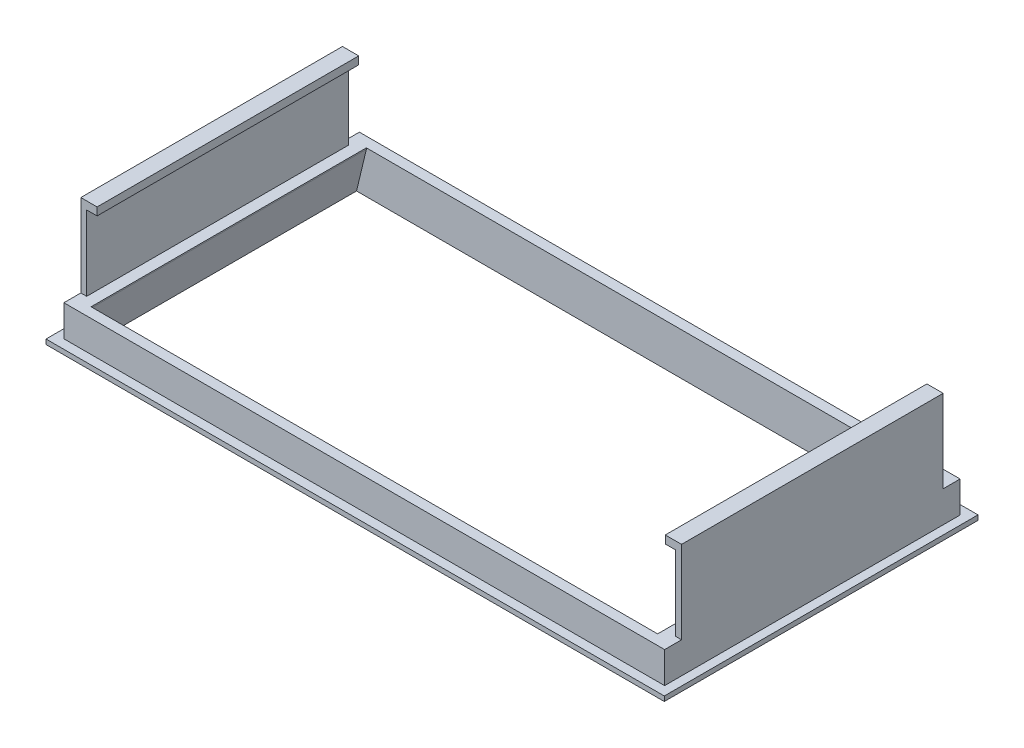
SolidWorks part; units mm, degrees
ref_plane "Front" through (0, 0, 0) normal (0, 0, 1) x (1, 0, 0)
ref_plane "Top" through (0, 0, 0) normal (0, 1, 0) x (1, 0, 0)
ref_plane "Right" through (0, 0, 0) normal (1, 0, 0) x (0, 0, -1)
sketch "Sketch1" plane through (0, 0, 0) normal (0, 1, 0) x (1, 0, 0)
  line L1 (-47.5, 24.1) -> (47.5, 24.1)
  line L2 (-47.5, 24.1) -> (-47.5, -24.1)
  line L3 (-47.5, -24.1) -> (47.5, -24.1)
  line L4 (47.5, 24.1) -> (47.5, -24.1)
  dimension "D1" = 95
  dimension "D2" = 48.2
  dimension "D3" = 24.1
  dimension "D4" = 47.5
extrude "Boss-Extrude2" add sketch "Sketch1" along normal blind 1.7
sketch "Sketch3" plane through (0, 1.7, 0) normal (0, 1, 0) x (1, 0, 0)
  line L1 (-46.15, 22.7) -> (46.15, 22.7)
  line L2 (-46.15, 22.7) -> (-46.15, -22.7)
  line L3 (-46.15, -22.7) -> (46.15, -22.7)
  line L4 (46.15, 22.7) -> (46.15, -22.7)
  dimension "D1" = 45.4
  dimension "D2" = 92.3
  dimension "D3" = 46.15
  dimension "D4" = 22.7
extrude "Boss-Extrude3" add sketch "Sketch3" along normal blind 4.8
sketch "Sketch4" plane through (0, 6.5, 0) normal (0, 1, 0) x (-1, 0, 0)
  line L1 (43.525, -21.15) -> (-43.525, -21.15)
  line L2 (43.525, -21.15) -> (43.525, 21.15)
  line L3 (43.525, 21.15) -> (-43.525, 21.15)
  line L4 (-43.525, -21.15) -> (-43.525, 21.15)
  dimension "D1" = 42.3
  dimension "D2" = 21.15
  dimension "D3" = 87.05
  dimension "D4" = 43.525
extrude "Cut-Extrude1" cut sketch "Sketch4" against normal through all
chamfer "Chamfer1" distance 0.96 angle 45 1 edges at (47.5, 0, 0)
chamfer "Chamfer2" distance 0.96 angle 45 1 edges at (-0.48, 0, -24.1)
chamfer "Chamfer3" distance 0.96 angle 45 1 edges at (-47.5, 0, 0.48)
chamfer "Chamfer4" distance 0.96 angle 45 1 edges at (0, 0, 24.1)
chamfer "Chamfer5" distance 6.31 distance2 1.51 1 edges at (-43.525, 0, 0)
chamfer "Chamfer6" distance 6.31 distance2 1.51 1 edges at (43.525, 0, 0)
sketch "Sketch5" plane through (0, 6.5, 0) normal (0, 1, 0) x (1, 0, 0)
  line L1 (-46.15, 20.1) -> (46.15, 20.1)
  line L2 (-46.15, 20.1) -> (-46.15, -20.1)
  line L3 (-46.15, -20.1) -> (46.15, -20.1)
  line L4 (46.15, 20.1) -> (46.15, -20.1)
  dimension "D1" = 40.2
  dimension "D2" = 20.1
  dimension "D3" = 92.3
  dimension "D4" = 46.15
extrude "Boss-Extrude11" add sketch "Sketch5" along normal blind 11.5
sketch "Sketch6" plane through (0, 18, 0) normal (0, 1, 0) x (1, 0, 0)
  line L1 (-45.25, 20.1) -> (45.25, 20.1)
  line L2 (-45.25, 20.1) -> (-45.25, -20.1)
  line L3 (-45.25, -20.1) -> (45.25, -20.1)
  line L4 (45.25, 20.1) -> (45.25, -20.1)
  dimension "D1" = 40.2
  dimension "D2" = 90.5
  dimension "D3" = 45.25
  dimension "D4" = 20.1
extrude "Cut-Extrude2" cut sketch "Sketch6" against normal blind 11.5
sketch "Sketch7" plane through (0, 18, 0) normal (0, 1, 0) x (-1, 0, 0)
  line L0 (46.15, -20.1) -> (46.15, 20.1) construction
  line L1 (46.15, -20.1) -> (-46.15, -20.1)
  line L2 (46.15, -20.1) -> (46.15, 20.1)
  line L3 (46.15, 20.1) -> (-46.15, 20.1)
  line L4 (-46.15, -20.1) -> (-46.15, 20.1)
  dimension "D1" = 92.3
  dimension "D2" = 40.2
  dimension "D3" = 20.1
extrude "Boss-Extrude12" add sketch "Sketch7" along normal blind 1.2
sketch "Sketch8" plane through (0, 19.2, 0) normal (0, 1, 0) x (1, 0, 0)
  line L1 (-43.65, 20.1) -> (43.65, 20.1)
  line L2 (-43.65, 20.1) -> (-43.65, -20.1)
  line L3 (-43.65, -20.1) -> (43.65, -20.1)
  line L4 (43.65, 20.1) -> (43.65, -20.1)
  dimension "D1" = 40.2
  dimension "D2" = 20.1
  dimension "D3" = 43.65
  dimension "D4" = 43.65
extrude "Cut-Extrude3" cut sketch "Sketch8" against normal blind 1.2
